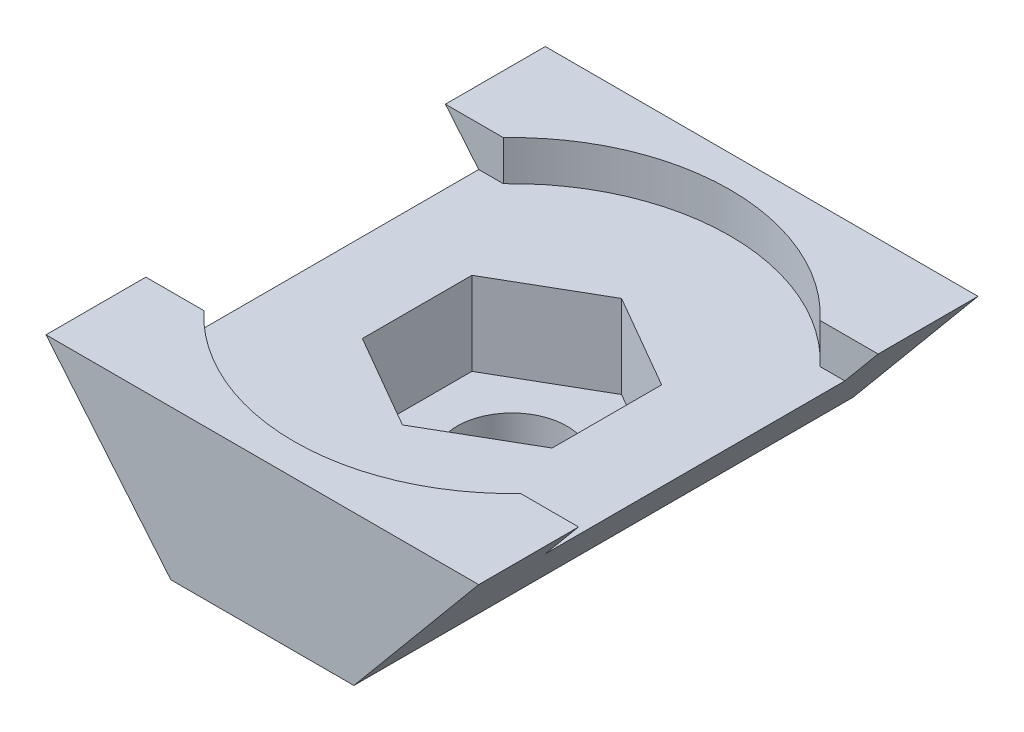
SolidWorks part; units mm, degrees
ref_plane "Plano frontal" through (0, 0, 0) normal (0, 0, 1) x (1, 0, 0)
ref_plane "Plano superior" through (0, 0, 0) normal (0, 1, 0) x (1, 0, 0)
ref_plane "Plano direito" through (0, 0, 0) normal (1, 0, 0) x (0, 0, -1)
sketch "Esboço1" plane through (0, 0, 0) normal (0, 0, 1) x (1, 0, 0)
  line L0 (-6.5, 0) -> (6.5, 0)
  line L1 (6.5, 0) -> (2.75, -4.5)
  line L2 (2.75, -4.5) -> (-2.75, -4.5)
  line L3 (-2.75, -4.5) -> (-6.5, 0)
  line L4 (0, 0) -> (0, -7.459) construction
  point P4 (0, 0)
  point P8 (0, 0)
  point P9 (-3.1149, -3.6923)
  dimension "D1" = 13
  dimension "D2" = 4.5
  dimension "D3" = 5.5
extrude "Ressalto-extrusão1" add sketch "Esboço1" along normal blind 15 contours L0 L1 L2 L3
sketch "Esboço2" plane through (0, 0, 0) normal (0, 1, 0) x (1, 0, 0)
  line L0 (-6.5, -15) -> (-6.5, 0) construction
  circle A0 centre (0, -7.5) radius 1.65
  point P2 (0, 0)
  point P5 (-6.5, -7.5)
  point P6 (0, 0)
  dimension "D1" = 3.3
extrude "Corte-extrusão1" cut sketch "Esboço2" against normal blind 15
sketch "Esboço3" plane through (0, 0, 0) normal (0, 1, 0) x (1, 0, 0)
  line L0 (4.7595, -3) -> (7.8136, -3)
  line L1 (-7.8136, -12) -> (-4.7595, -12)
  line L2 (-7.8136, -12) -> (-7.8136, -3)
  line L3 (-7.8136, -3) -> (-4.7595, -3)
  line L4 (7.8136, -12) -> (7.8136, -3)
  line L5 (-7.8136, -12) -> (7.8136, -3) construction
  line L6 (-7.8136, -3) -> (7.8136, -12) construction
  line L7 (4.7595, -12) -> (7.8136, -12)
  arc A0 (-4.7595, -12) -> (4.7595, -12) centre (0, -7.5) ccw
  arc A1 (4.7595, -3) -> (-4.7595, -3) centre (0, -7.5) ccw
  point P10 (-7.8136, -2.9035)
  dimension "D1" = 13.1
  dimension "D2" = 9
extrude "Corte-extrusão5" cut sketch "Esboço3" against normal blind 1.2 contours A0 L7 L4 L0 A1 L3 L2 L1
sketch "Esboço4" plane through (0, -1.2, 0) normal (0, 1, 0) x (1, 0, 0)
  line L1 (0, -4.2091) -> (-2.85, -5.8546)
  line L2 (-2.85, -5.8546) -> (-2.85, -9.1454)
  line L3 (-2.85, -9.1454) -> (0, -10.7909)
  line L4 (0, -10.7909) -> (2.85, -9.1454)
  line L5 (2.85, -9.1454) -> (2.85, -5.8546)
  line L6 (2.85, -5.8546) -> (0, -4.2091)
  circle A0 centre (0, -7.5) radius 2.85 construction
  dimension "D1" = 5.7
extrude "Corte-extrusão6" cut sketch "Esboço4" against normal blind 2.5
